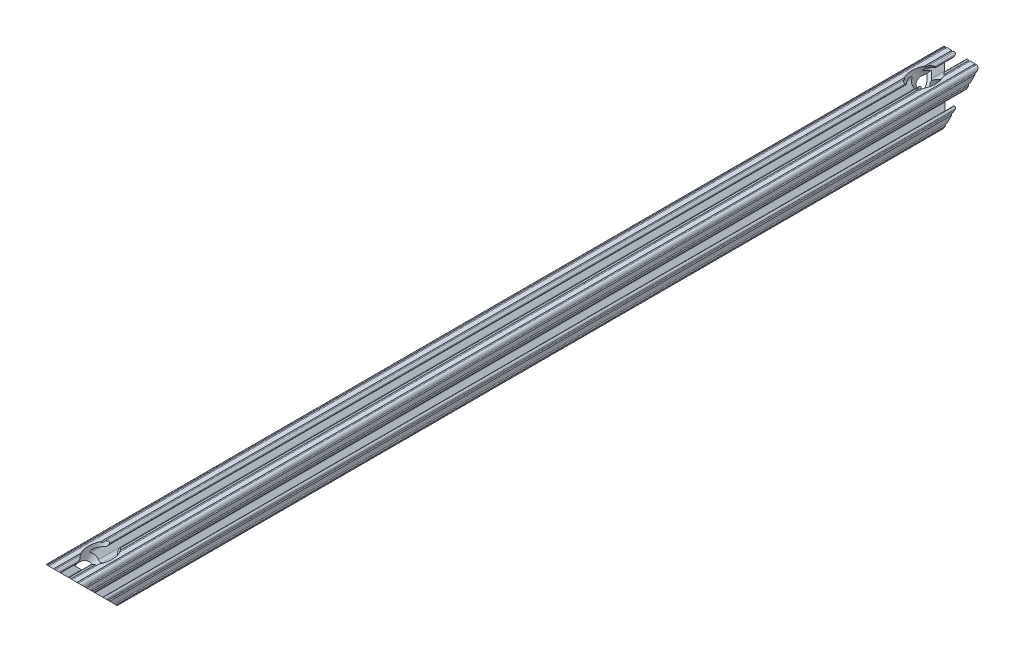
SolidWorks part; units mm, degrees
ref_plane "Front Plane" through (0, 0, 0) normal (0, 0, 1) x (1, 0, 0)
ref_plane "Top Plane" through (0, 0, 0) normal (0, 1, 0) x (1, 0, 0)
ref_plane "Right Plane" through (0, 0, 0) normal (1, 0, 0) x (0, 0, -1)
sketch "Sketch1" plane through (0, 0, 0) normal (0, 0, 1) x (1, 0, 0)
  line L2 (-7.1797, -8.6452) -> (-3.9523, -5.4237)
  line L3 (-1.7093, -4.4958) -> (1.7093, -4.4958)
  line L4 (3.9523, -5.4237) -> (7.1797, -8.6452)
  line L6 (6.4164, -10.4902) -> (4.2875, -10.4902)
  line L7 (3.2385, -11.5392) -> (3.2385, -11.651)
  line L8 (4.2875, -12.7) -> (5.3171, -12.7)
  line L9 (6.3331, -12.7) -> (9.5504, -12.7)
  line L10 (12.7, -9.5504) -> (12.7, -6.3331)
  line L11 (12.7, -5.3171) -> (12.7, -4.2875)
  line L12 (11.651, -3.2385) -> (11.5392, -3.2385)
  line L13 (10.4902, -4.2875) -> (10.4902, -6.4021)
  line L14 (8.7371, -7.1294) -> (5.441, -3.8408)
  line L15 (4.5085, -1.5932) -> (4.5085, 1.5932)
  line L16 (5.441, 3.8408) -> (8.7371, 7.1294)
  line L17 (10.4902, 6.4021) -> (10.4902, 4.2875)
  line L18 (11.5392, 3.2385) -> (11.651, 3.2385)
  line L19 (12.7, 4.2875) -> (12.7, 5.3171)
  line L20 (12.7, 6.3331) -> (12.7, 9.5504)
  line L21 (9.5504, 12.7) -> (6.3331, 12.7)
  line L22 (5.3171, 12.7) -> (4.2875, 12.7)
  line L23 (3.2385, 11.651) -> (3.2385, 11.5392)
  line L24 (4.2875, 10.4902) -> (6.4768, 10.4902)
  line L25 (7.207, 8.7244) -> (3.8983, 5.4232)
  line L26 (1.6558, 4.4958) -> (-1.6558, 4.4958)
  line L27 (-3.8983, 5.4232) -> (-7.207, 8.7244)
  line L28 (-6.4768, 10.4902) -> (-4.2875, 10.4902)
  line L29 (-3.2385, 11.5392) -> (-3.2385, 11.651)
  line L30 (-4.2875, 12.7) -> (-5.3171, 12.7)
  line L31 (-6.3331, 12.7) -> (-9.5504, 12.7)
  line L32 (-12.7, 9.5504) -> (-12.7, 6.3331)
  line L33 (-12.7, 5.3171) -> (-12.7, 4.2875)
  line L34 (-11.651, 3.2385) -> (-11.5392, 3.2385)
  line L35 (-10.4902, 4.2875) -> (-10.4902, 6.4021)
  line L36 (-8.7371, 7.1294) -> (-5.441, 3.8408)
  line L37 (-4.5085, 1.5932) -> (-4.5085, -1.5932)
  line L38 (-5.441, -3.8408) -> (-8.7371, -7.1294)
  line L39 (-10.4902, -6.4021) -> (-10.4902, -4.2875)
  line L40 (-11.5392, -3.2385) -> (-11.651, -3.2385)
  line L41 (-12.7, -4.2875) -> (-12.7, -5.3171)
  line L42 (-12.7, -6.3331) -> (-12.7, -9.5504)
  line L43 (-9.5504, -12.7) -> (-6.3331, -12.7)
  line L44 (-5.3171, -12.7) -> (-4.2875, -12.7)
  line L45 (-3.2385, -11.651) -> (-3.2385, -11.5392)
  line L46 (-4.2875, -10.4902) -> (-6.4164, -10.4902)
  circle A0 centre (0, 0) radius 2.6035
  arc A1 (-7.1797, -8.6452) -> (-6.4164, -10.4902) centre (-6.4164, -9.4098) ccw
  arc A2 (-1.7093, -4.4958) -> (-3.9523, -5.4237) centre (-1.7093, -7.6708) ccw
  arc A3 (3.9523, -5.4237) -> (1.7093, -4.4958) centre (1.7093, -7.6708) ccw
  arc A4 (6.4164, -10.4902) -> (7.1797, -8.6452) centre (6.4164, -9.4098) ccw
  arc A5 (4.2875, -10.4902) -> (3.2385, -11.5392) centre (4.2875, -11.5392) ccw
  arc A6 (3.2385, -11.651) -> (4.2875, -12.7) centre (4.2875, -11.651) ccw
  arc A7 (6.3331, -12.7) -> (5.3171, -12.7) centre (5.8251, -12.7) ccw
  arc A8 (10.5664, -12.6998) -> (9.5504, -12.7) centre (10.0584, -12.7) ccw
  arc A9 (10.5664, -12.6998) -> (12.6998, -10.5664) centre (10.5918, -10.5918) ccw
  arc A10 (12.7, -9.5504) -> (12.6998, -10.5664) centre (12.7, -10.0584) ccw
  arc A11 (12.7, -5.3171) -> (12.7, -6.3331) centre (12.7, -5.8251) ccw
  arc A12 (12.7, -4.2875) -> (11.651, -3.2385) centre (11.651, -4.2875) ccw
  arc A13 (11.5392, -3.2385) -> (10.4902, -4.2875) centre (11.5392, -4.2875) ccw
  arc A14 (8.7371, -7.1294) -> (10.4902, -6.4021) centre (9.4628, -6.4021) ccw
  arc A15 (4.5085, -1.5932) -> (5.441, -3.8408) centre (7.6835, -1.5932) ccw
  arc A16 (5.441, 3.8408) -> (4.5085, 1.5932) centre (7.6835, 1.5932) ccw
  arc A17 (10.4902, 6.4021) -> (8.7371, 7.1294) centre (9.4628, 6.4021) ccw
  arc A18 (10.4902, 4.2875) -> (11.5392, 3.2385) centre (11.5392, 4.2875) ccw
  arc A19 (11.651, 3.2385) -> (12.7, 4.2875) centre (11.651, 4.2875) ccw
  arc A20 (12.7, 6.3331) -> (12.7, 5.3171) centre (12.7, 5.8251) ccw
  arc A21 (12.6998, 10.5664) -> (12.7, 9.5504) centre (12.7, 10.0584) ccw
  arc A22 (12.6998, 10.5664) -> (10.5664, 12.6998) centre (10.5918, 10.5918) ccw
  arc A23 (9.5504, 12.7) -> (10.5664, 12.6998) centre (10.0584, 12.7) ccw
  arc A24 (5.3171, 12.7) -> (6.3331, 12.7) centre (5.8251, 12.7) ccw
  arc A25 (4.2875, 12.7) -> (3.2385, 11.651) centre (4.2875, 11.651) ccw
  arc A26 (3.2385, 11.5392) -> (4.2875, 10.4902) centre (4.2875, 11.5392) ccw
  arc A27 (7.207, 8.7244) -> (6.4768, 10.4902) centre (6.4768, 9.4563) ccw
  arc A28 (1.6558, 4.4958) -> (3.8983, 5.4232) centre (1.6558, 7.6708) ccw
  arc A29 (-3.8983, 5.4232) -> (-1.6558, 4.4958) centre (-1.6558, 7.6708) ccw
  arc A30 (-6.4768, 10.4902) -> (-7.207, 8.7244) centre (-6.4768, 9.4563) ccw
  arc A31 (-4.2875, 10.4902) -> (-3.2385, 11.5392) centre (-4.2875, 11.5392) ccw
  arc A32 (-3.2385, 11.651) -> (-4.2875, 12.7) centre (-4.2875, 11.651) ccw
  arc A33 (-6.3331, 12.7) -> (-5.3171, 12.7) centre (-5.8251, 12.7) ccw
  arc A34 (-10.5664, 12.6998) -> (-9.5504, 12.7) centre (-10.0584, 12.7) ccw
  arc A35 (-10.5664, 12.6998) -> (-12.6998, 10.5664) centre (-10.5918, 10.5918) ccw
  arc A36 (-12.7, 9.5504) -> (-12.6998, 10.5664) centre (-12.7, 10.0584) ccw
  arc A37 (-12.7, 5.3171) -> (-12.7, 6.3331) centre (-12.7, 5.8251) ccw
  arc A38 (-12.7, 4.2875) -> (-11.651, 3.2385) centre (-11.651, 4.2875) ccw
  arc A39 (-11.5392, 3.2385) -> (-10.4902, 4.2875) centre (-11.5392, 4.2875) ccw
  arc A40 (-8.7371, 7.1294) -> (-10.4902, 6.4021) centre (-9.4628, 6.4021) ccw
  arc A41 (-4.5085, 1.5932) -> (-5.441, 3.8408) centre (-7.6835, 1.5932) ccw
  arc A42 (-5.441, -3.8408) -> (-4.5085, -1.5932) centre (-7.6835, -1.5932) ccw
  arc A43 (-10.4902, -6.4021) -> (-8.7371, -7.1294) centre (-9.4628, -6.4021) ccw
  arc A44 (-10.4902, -4.2875) -> (-11.5392, -3.2385) centre (-11.5392, -4.2875) ccw
  arc A45 (-11.651, -3.2385) -> (-12.7, -4.2875) centre (-11.651, -4.2875) ccw
  arc A46 (-12.7, -6.3331) -> (-12.7, -5.3171) centre (-12.7, -5.8251) ccw
  arc A47 (-12.6998, -10.5664) -> (-12.7, -9.5504) centre (-12.7, -10.0584) ccw
  arc A48 (-12.6998, -10.5664) -> (-10.5664, -12.6998) centre (-10.5918, -10.5918) ccw
  arc A49 (-9.5504, -12.7) -> (-10.5664, -12.6998) centre (-10.0584, -12.7) ccw
  arc A50 (-5.3171, -12.7) -> (-6.3331, -12.7) centre (-5.8251, -12.7) ccw
  arc A51 (-4.2875, -12.7) -> (-3.2385, -11.651) centre (-4.2875, -11.651) ccw
  arc A52 (-3.2385, -11.5392) -> (-4.2875, -10.4902) centre (-4.2875, -11.5392) ccw
extrude "Boss-Extrude1" add sketch "Sketch1" along normal mid plane 609.6
sketch "Sketch2" plane through (0, 0, 0) normal (1, 0, 0) x (0, 0, -1)
  line L0 (-304.8, 12.6998) -> (-304.8, -12.7)
  line L1 (-304.8, -12.7) -> (-279.4002, -12.7)
  line L2 (-279.4002, -12.7) -> (-304.8, 12.6998)
  line L3 (0, 0) -> (0, -12.7) construction
  line L5 (279.4002, -12.7) -> (304.8, 12.6998)
  line L6 (304.8, -12.7) -> (279.4002, -12.7)
  line L7 (304.8, 12.6998) -> (304.8, -12.7)
  line L8 (-304.8, -12.7) -> (304.8, -12.7) construction
extrude "Cut-Extrude1" cut sketch "Sketch2" against normal through all and the other way through all
sketch "Sketch3" plane through (0, 0, 0) normal (1, 0, 0) x (0, 0, -1)
  line L0 (-273.7876, 18.3125) -> (-292.1002, 0)
  line L1 (-292.1002, 0) -> (-294.4081, 2.3079)
  line L2 (-294.4081, 2.3079) -> (-289.918, 6.7981)
  line L3 (-289.918, 6.7981) -> (-293.2227, 10.1028)
  line L4 (-293.2227, 10.1028) -> (-279.4003, 23.9252)
  line L5 (-279.4003, 23.9252) -> (-273.7876, 18.3125)
  line L6 (-292.1002, 0) -> (-294.4081, -2.3079) construction
  line L7 (-279.4002, -12.7) -> (-304.8, 12.6998) construction
  line L8 (-294.7037, 2.6035) -> (-289.4967, -2.6035) construction
  line L9 (-281.9974, -1.1225) -> (-268.175, 12.6998) construction
  dimension "D1" = 6.5278
  dimension "D2" = 15.875
  dimension "D3" = 6.35
revolve "Cut-Revolve1" cut sketch "Sketch3" angle 360 mid plane about L6
mirror "Mirror1" about plane through (0, 0, 0) normal (0, 0, 1) of "Cut-Revolve1"
